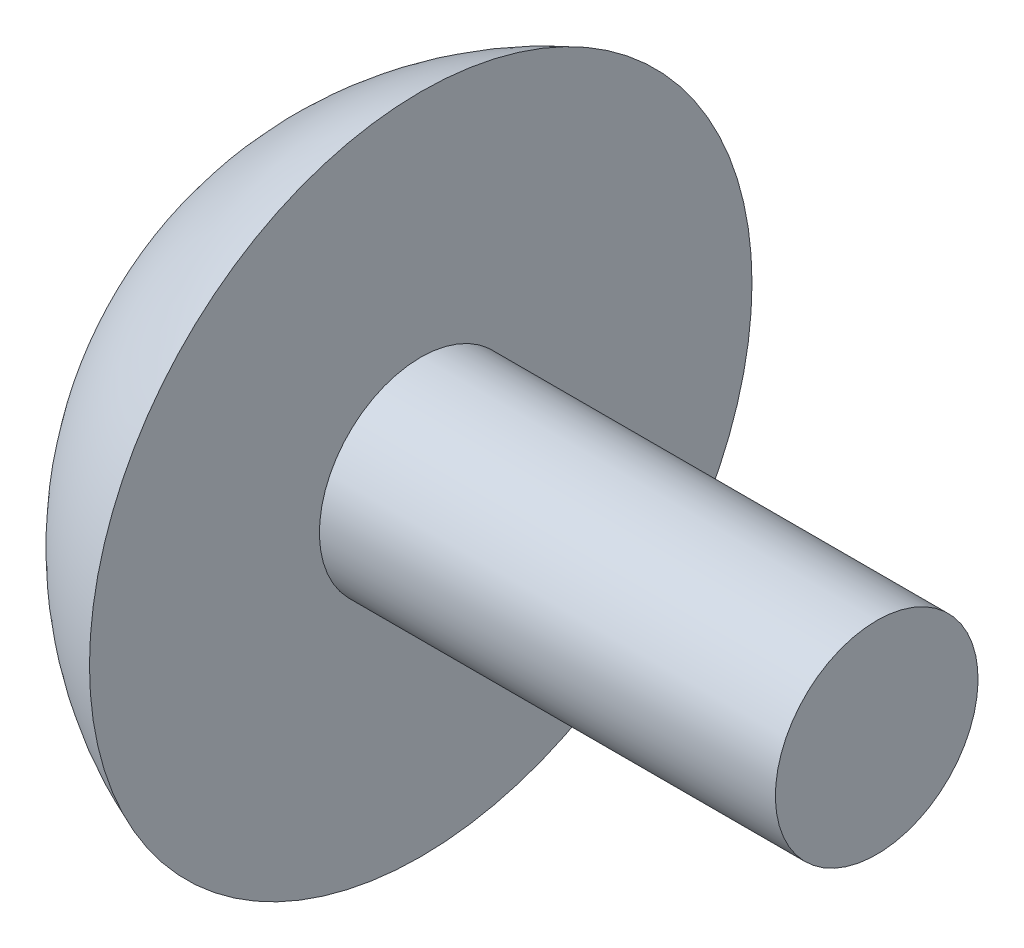
SolidWorks part; units mm, degrees
ref_plane "Plan de face" through (0, 0, 0) normal (0, 0, 1) x (1, 0, 0)
ref_plane "Plan de dessus" through (0, 0, 0) normal (0, 1, 0) x (1, 0, 0)
ref_plane "Plan de droite" through (0, 0, 0) normal (1, 0, 0) x (0, 0, -1)
sketch "Esquisse5" plane through (0, 0, 0) normal (0, 0, 1) x (1, 0, 0)
  line L0 (0, 0) -> (-13.5, 0)
  line L1 (0, 0) -> (0, -2)
  line L2 (0, -2) -> (-9, -2)
  line L3 (-9, -2) -> (-9, -6.5383)
  arc A0 (-13.5, 0) -> (-9, -6.5383) centre (-6.5, 0) ccw
  dimension "D1" = 7
  dimension "D2" = 13.5
  dimension "D3" = 2
  dimension "D4" = 9
revolve "Révolution2" add sketch "Esquisse5" angle 360 about L0
